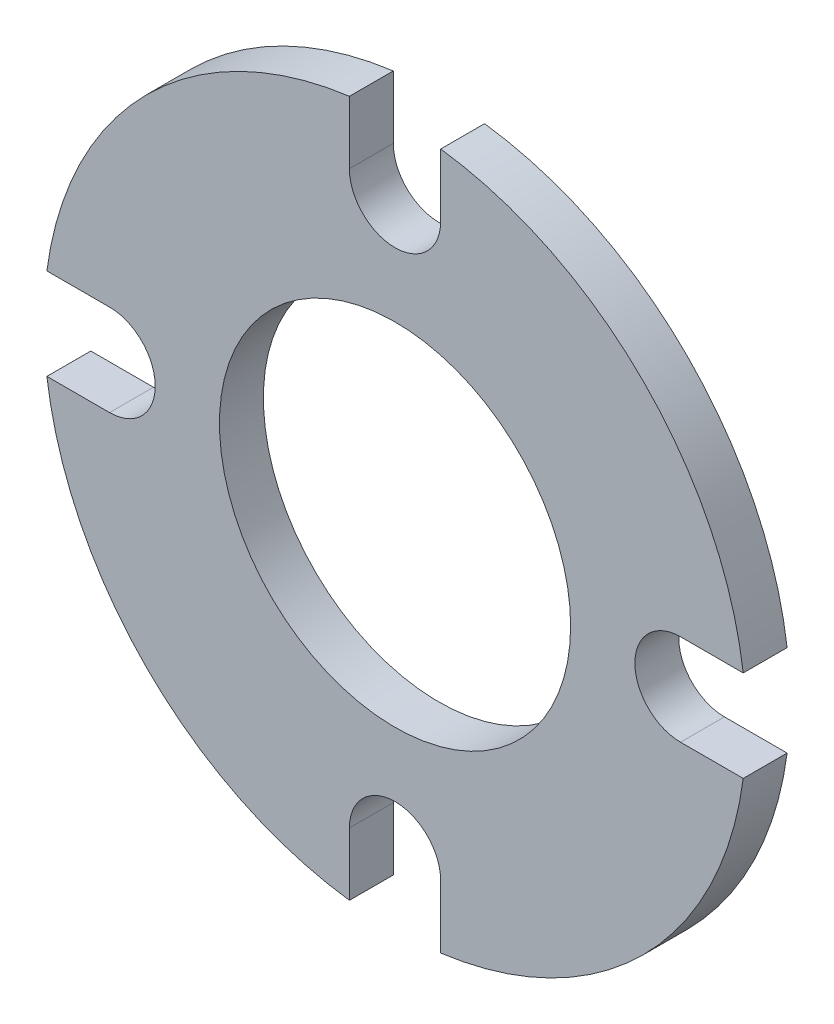
SolidWorks part; units mm, degrees
ref_plane "Front Plane" through (0, 0, 0) normal (0, 0, 1) x (1, 0, 0)
ref_plane "Top Plane" through (0, 0, 0) normal (0, 1, 0) x (1, 0, 0)
ref_plane "Right Plane" through (0, 0, 0) normal (1, 0, 0) x (0, 0, -1)
sketch "Sketch1" plane through (0, 0, 0) normal (0, 0, 1) x (1, 0, 0)
  line L0 (1.3718, 0) -> (-1.4142, 0) construction
  line L1 (-0.813, 0.13) -> (-0.9915, 0.13)
  line L2 (0.13, 0.813) -> (0.13, 0.9915)
  line L3 (-0.9915, -0.13) -> (-0.813, -0.13)
  line L4 (-0.13, 0.9915) -> (-0.13, 0.813)
  line L5 (0.813, -0.13) -> (0.9915, -0.13)
  line L6 (0.9915, 0.13) -> (0.813, 0.13)
  line L7 (-0.13, -0.813) -> (-0.13, -0.9915)
  line L8 (0.13, -0.9915) -> (0.13, -0.813)
  arc A0 (-0.9915, -0.13) -> (-0.13, -0.9915) centre (0, 0) ccw
  circle A1 centre (0, 0) radius 0.5
  arc A2 (-0.813, -0.13) -> (-0.813, 0.13) centre (-0.813, 0) ccw
  arc A3 (-0.13, 0.813) -> (0.13, 0.813) centre (0, 0.813) ccw
  arc A4 (0.813, 0.13) -> (0.813, -0.13) centre (0.813, 0) ccw
  arc A5 (0.13, -0.813) -> (-0.13, -0.813) centre (0, -0.813) ccw
  arc A6 (0.13, -0.9915) -> (0.9915, -0.13) centre (0, 0) ccw
  arc A7 (0.9915, 0.13) -> (0.13, 0.9915) centre (0, 0) ccw
  arc A8 (-0.13, 0.9915) -> (-0.9915, 0.13) centre (0, 0) ccw
  point P1 (0, 0)
  point P7 (0, 0)
  point P28 (0, 0)
  dimension "D1" = 2
  dimension "D2" = 1
  dimension "D3" = 0.13
  dimension "D4" = 0.813
  dimension "D5" = 4
extrude "Boss-Extrude1" add sketch "Sketch1" along normal blind 0.125
